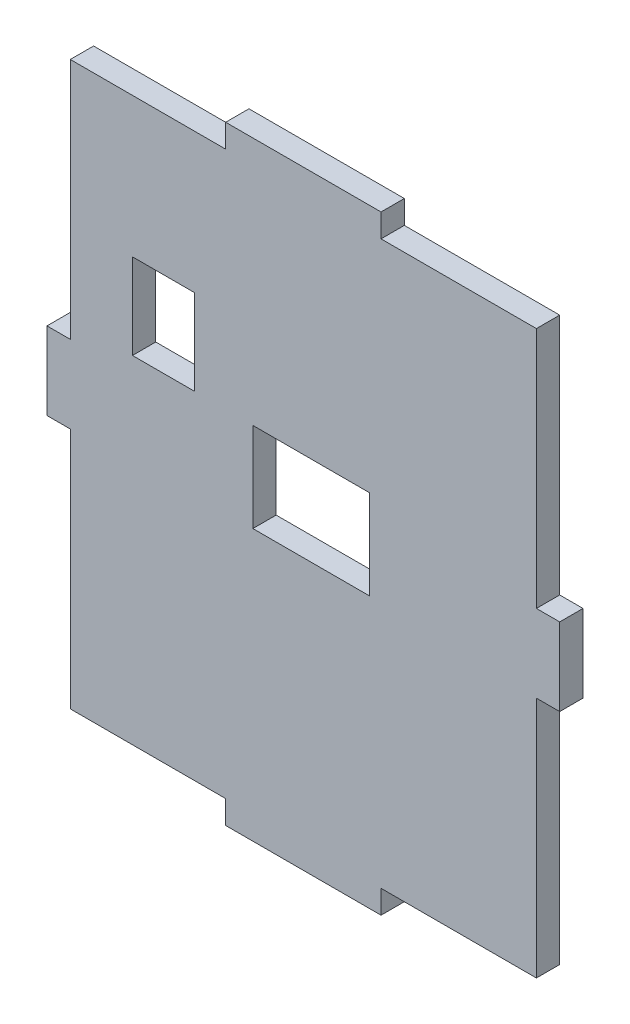
SolidWorks part; units mm, degrees
ref_plane "Front Plane" through (0, 0, 0) normal (0, 0, 1) x (1, 0, 0)
ref_plane "Top Plane" through (0, 0, 0) normal (0, 1, 0) x (1, 0, 0)
ref_plane "Right Plane" through (0, 0, 0) normal (1, 0, 0) x (0, 0, -1)
sketch "Model" plane through (0, 0, 0) normal (0, 0, 1) x (1, 0, 0)
  line L0 (-62.6818, -45.5455) -> (-47.6818, -45.5455)
  line L1 (-47.6818, -45.5455) -> (-47.6818, -34.0455)
  line L2 (-47.6818, -34.0455) -> (-62.6818, -34.0455)
  line L3 (-62.6818, -34.0455) -> (-62.6818, -45.5455)
  line L4 (-66.1818, -2) -> (-66.1818, -5)
  line L5 (-46.1818, -2) -> (-66.1818, -2)
  line L6 (-46.1818, -5) -> (-46.1818, -2)
  line L7 (-26.1818, -5) -> (-46.1818, -5)
  line L8 (-26.1818, -36.2) -> (-26.1818, -5)
  line L9 (-23.1818, -36.2) -> (-26.1818, -36.2)
  line L10 (-23.1818, -46.2) -> (-23.1818, -36.2)
  line L11 (-26.1818, -46.2) -> (-23.1818, -46.2)
  line L12 (-26.1818, -77.4) -> (-26.1818, -46.2)
  line L13 (-46.1818, -77.4) -> (-26.1818, -77.4)
  line L14 (-46.1818, -80.4) -> (-46.1818, -77.4)
  line L15 (-66.1818, -80.4) -> (-46.1818, -80.4)
  line L16 (-66.1818, -77.4) -> (-66.1818, -80.4)
  line L17 (-86.1818, -77.4) -> (-66.1818, -77.4)
  line L18 (-86.1818, -46.2) -> (-86.1818, -77.4)
  line L19 (-89.1818, -46.2) -> (-86.1818, -46.2)
  line L20 (-89.1818, -36.2) -> (-89.1818, -46.2)
  line L21 (-86.1818, -36.2) -> (-89.1818, -36.2)
  line L22 (-86.1818, -5) -> (-86.1818, -36.2)
  line L23 (-66.1818, -5) -> (-86.1818, -5)
  line L24 (-78.1818, -34) -> (-70.1818, -34)
  line L25 (-70.1818, -34) -> (-70.1818, -23)
  line L26 (-70.1818, -23) -> (-78.1818, -23)
  line L27 (-78.1818, -23) -> (-78.1818, -34)
  dimension "D1" = 8
  dimension "D2" = 8
  dimension "D3" = 3
  dimension "D4" = 3
  dimension "D5" = 31.2
  dimension "D6" = 11
  dimension "D7" = 15
  dimension "D8" = 3
  dimension "D9" = 3
  dimension "D10" = 31.2
  dimension "D11" = 3
  dimension "D12" = 18
  dimension "D13" = 20
  dimension "D14" = 20
  dimension "D15" = 78.4
  dimension "D16" = 41.2
  dimension "D17" = 72.4
  dimension "D18" = 23.5
  dimension "D19" = 3
  dimension "D20" = 31.2
  dimension "D21" = 10
  dimension "D22" = 31.2
  dimension "D23" = 10
  dimension "D24" = 66
  dimension "D25" = 21.5
extrude "Boss-Extrude1" add sketch "Model" along normal blind 3 contours L2 L3 L0 L1 | L26 L27 L24 L25 | L22 L21 L20 L19 L18 L17 L16 L15 L14 L13 L12 L11 L10 L9 L8 L7 L6 L5 L4 L23
